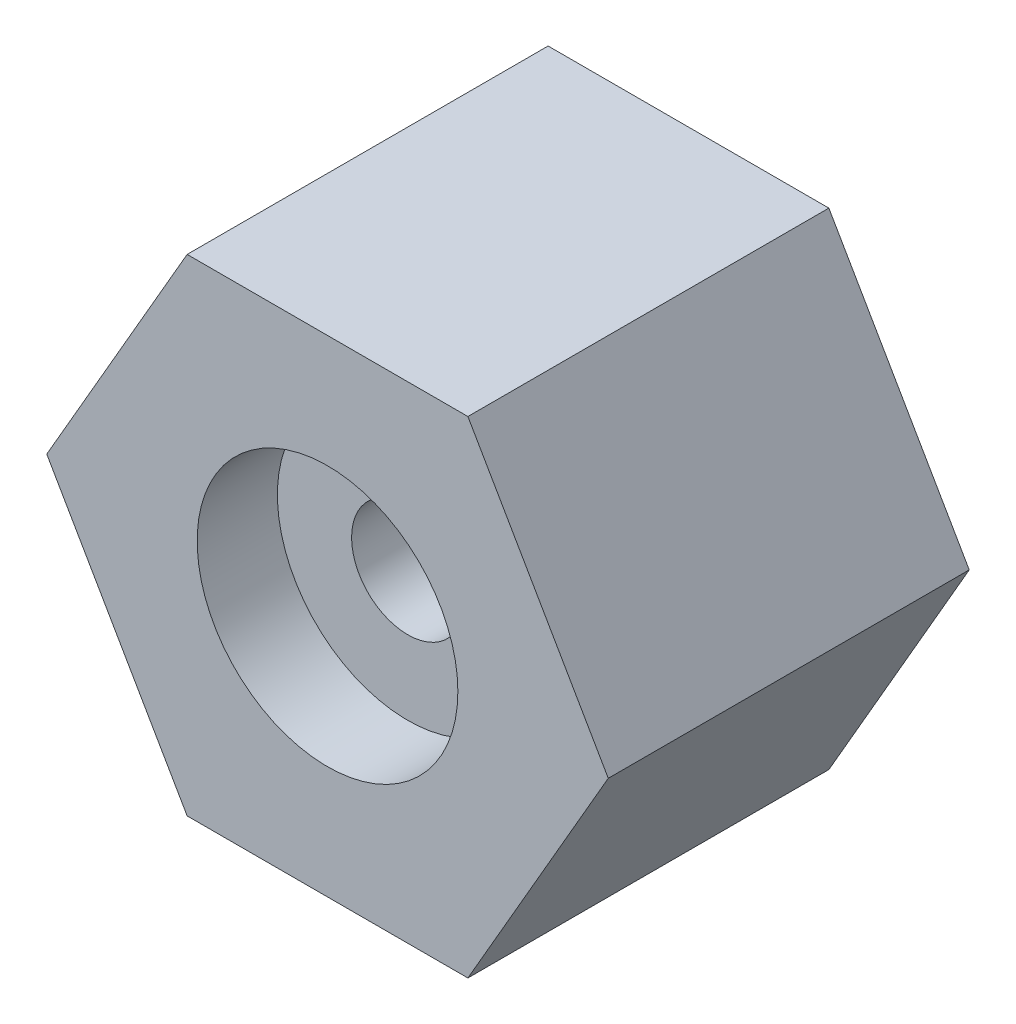
SolidWorks part; units mm, degrees
material "Plain Carbon Steel"
ref_plane "Front Plane" through (0, 0, 0) normal (0, 0, 1) x (1, 0, 0)
ref_plane "Top Plane" through (0, 0, 0) normal (0, 1, 0) x (1, 0, 0)
ref_plane "Right Plane" through (0, 0, 0) normal (1, 0, 0) x (0, 0, -1)
sketch "Sketch1" plane through (0, 0, 0) normal (0, 0, 1) x (1, 0, 0)
  line L8 (-17.5, 30.3109) -> (17.5, 30.3109)
  line L9 (17.5, 30.3109) -> (35, 0)
  line L10 (35, 0) -> (17.5, -30.3109)
  line L11 (17.5, -30.3109) -> (-17.5, -30.3109)
  line L12 (-17.5, -30.3109) -> (-35, 0)
  line L13 (-35, 0) -> (-17.5, 30.3109)
  circle A0 centre (0, 0) radius 35 construction
  dimension "D1" = 35
extrude "Boss-Extrude1" add sketch "Sketch1" along normal mid plane 45
sketch "Sketch2" plane through (0, 0, 22.5) normal (0, 0, 1) x (1, 0, 0)
  circle A0 centre (0, 0) radius 16.25
  dimension "D1" = 32.5
extrude "Cut-Extrude1" cut sketch "Sketch2" against normal blind 10
mirror "Mirror1" about plane through (0, 0, 0) normal (0, 0, 1) of "Cut-Extrude1"
sketch "Sketch3" plane through (0, 0, -12.5) normal (0, 0, -1) x (-1, 0, 0)
  circle A0 centre (0, 0) radius 7
  dimension "D1" = 14
extrude "Cut-Extrude2" cut sketch "Sketch3" against normal up to surface (25 mm away) up to face at (16.25, 0, 12.5)
